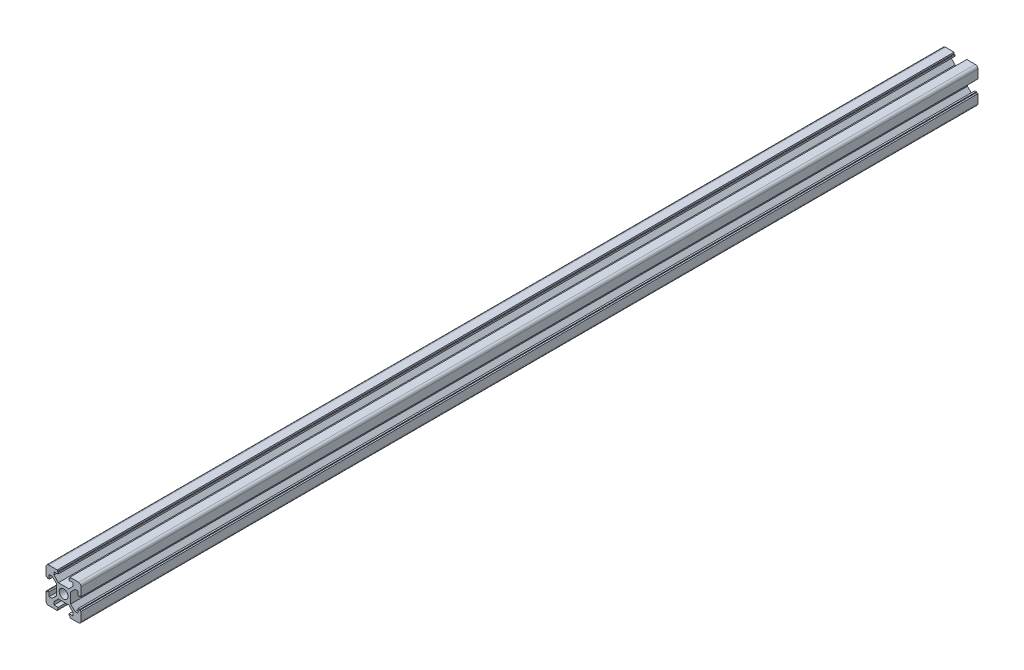
SolidWorks part; units mm, degrees
ref_plane "前视基准面" through (0, 0, 0) normal (0, 0, 1) x (1, 0, 0)
ref_plane "上视基准面" through (0, 0, 0) normal (0, 1, 0) x (1, 0, 0)
ref_plane "右视基准面" through (0, 0, 0) normal (1, 0, 0) x (0, 0, -1)
sketch "草图1" plane through (0, 0, 0) normal (0, 0, 1) x (1, 0, 0)
  line L0 (0, 0) -> (0, 12.7114) construction
  line L1 (0, 0) -> (12.7618, 0) construction
  line L2 (-3.0125, 4) -> (3.0125, 4)
  line L3 (0, 0) -> (12.1278, 12.1278) construction
  line L4 (3.0125, 4) -> (5.45, 6.5847)
  line L5 (5.45, 6.5847) -> (5.45, 8.2)
  line L6 (5.45, 8.2) -> (3.1, 8.2)
  line L7 (3.1, 8.2) -> (3.1, 9.1)
  line L8 (3.1, 9.1) -> (3.6, 9.1)
  line L9 (3.6, 9.1) -> (3.6, 10)
  line L10 (3.6, 10) -> (10, 10)
  line L11 (10, 3.6) -> (10, 10)
  line L12 (9.1, 3.6) -> (10, 3.6)
  line L13 (9.1, 3.1) -> (9.1, 3.6)
  line L14 (8.2, 3.1) -> (9.1, 3.1)
  line L15 (8.2, 5.45) -> (8.2, 3.1)
  line L16 (6.5847, 5.45) -> (8.2, 5.45)
  line L17 (4, 3.0125) -> (6.5847, 5.45)
  line L18 (4, -3.0125) -> (4, 3.0125)
  line L19 (4, -3.0125) -> (6.5847, -5.45)
  line L20 (6.5847, -5.45) -> (8.2, -5.45)
  line L21 (8.2, -5.45) -> (8.2, -3.1)
  line L22 (8.2, -3.1) -> (9.1, -3.1)
  line L23 (9.1, -3.1) -> (9.1, -3.6)
  line L24 (9.1, -3.6) -> (10, -3.6)
  line L25 (10, -3.6) -> (10, -10)
  line L26 (3.6, -10) -> (10, -10)
  line L27 (3.6, -9.1) -> (3.6, -10)
  line L28 (3.1, -9.1) -> (3.6, -9.1)
  line L29 (3.1, -8.2) -> (3.1, -9.1)
  line L30 (5.45, -8.2) -> (3.1, -8.2)
  line L31 (5.45, -6.5847) -> (5.45, -8.2)
  line L32 (3.0125, -4) -> (5.45, -6.5847)
  line L33 (-3.0125, -4) -> (3.0125, -4)
  line L34 (-3.0125, -4) -> (-5.45, -6.5847)
  line L35 (-5.45, -6.5847) -> (-5.45, -8.2)
  line L36 (-5.45, -8.2) -> (-3.1, -8.2)
  line L37 (-3.1, -8.2) -> (-3.1, -9.1)
  line L38 (-3.1, -9.1) -> (-3.6, -9.1)
  line L39 (-3.6, -9.1) -> (-3.6, -10)
  line L40 (-3.6, -10) -> (-10, -10)
  line L41 (-10, -3.6) -> (-10, -10)
  line L42 (-9.1, -3.6) -> (-10, -3.6)
  line L43 (-9.1, -3.1) -> (-9.1, -3.6)
  line L44 (-8.2, -3.1) -> (-9.1, -3.1)
  line L45 (-8.2, -5.45) -> (-8.2, -3.1)
  line L46 (-6.5847, -5.45) -> (-8.2, -5.45)
  line L47 (-4, -3.0125) -> (-6.5847, -5.45)
  line L48 (-4, -3.0125) -> (-4, 3.0125)
  line L49 (-4, 3.0125) -> (-6.5847, 5.45)
  line L50 (-6.5847, 5.45) -> (-8.2, 5.45)
  line L51 (-8.2, 5.45) -> (-8.2, 3.1)
  line L52 (-8.2, 3.1) -> (-9.1, 3.1)
  line L53 (-9.1, 3.1) -> (-9.1, 3.6)
  line L54 (-9.1, 3.6) -> (-10, 3.6)
  line L55 (-10, 3.6) -> (-10, 10)
  line L56 (-3.6, 10) -> (-10, 10)
  line L57 (-3.6, 9.1) -> (-3.6, 10)
  line L58 (-3.1, 9.1) -> (-3.6, 9.1)
  line L59 (-3.1, 8.2) -> (-3.1, 9.1)
  line L60 (-5.45, 8.2) -> (-3.1, 8.2)
  line L61 (-5.45, 6.5847) -> (-5.45, 8.2)
  line L62 (-3.0125, 4) -> (-5.45, 6.5847)
  circle A0 centre (0, 0) radius 2.5
  point P4 (5.2924, 4.2313)
  point P5 (-4, 0)
  point P24 (4, 0)
  point P40 (0, -4)
  point P69 (0, 4)
  dimension "D9" = 5
  dimension "D1" = 4
  dimension "D3" = 5.45
  dimension "D4" = 8.2
  dimension "D5" = 3.1
  dimension "D6" = 3.6
  dimension "D7" = 0.9
  dimension "D8" = 1.8
  dimension "D10" = 1.5
extrude "凸台-拉伸1" add sketch "草图1" along normal blind 510
fillet "圆角1" radius 1.5 4 edges at (10, -10, 255) (-10, -10, 255) (-10, 10, 255) (10, 10, 255)
